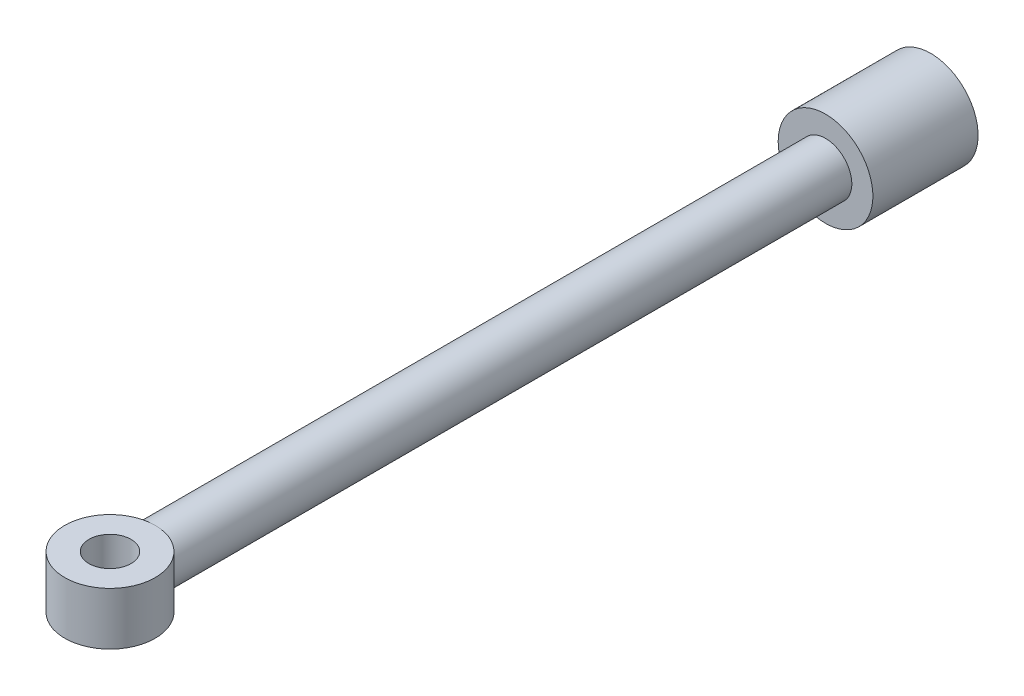
SolidWorks part; units mm, degrees
material "AISI 4340 Steel, normalized"
ref_plane "Front Plane" through (0, 0, 0) normal (0, 0, 1) x (1, 0, 0)
ref_plane "Top Plane" through (0, 0, 0) normal (0, 1, 0) x (1, 0, 0)
ref_plane "Right Plane" through (0, 0, 0) normal (1, 0, 0) x (0, 0, -1)
sketch "Sketch1" plane through (0, 0, 0) normal (0, 1, 0) x (1, 0, 0)
  line L0 (0, -75) -> (0, -855) construction
  line L1 (0, -75) -> (45, -75)
  line L4 (45, -75) -> (45, -175)
  line L5 (45, -175) -> (25, -175)
  line L6 (25, -175) -> (25, -820.0143)
  line L7 (25, -820.0143) -> (0, -820.0143)
  line L8 (0, -820.0143) -> (0, -75)
  circle A0 centre (0, -855) radius 20 construction
  circle A1 centre (0, -855) radius 43 construction
  circle A2 centre (0, 0) radius 20 construction
  dimension "D1" = 86
  dimension "D2" = 780
  dimension "D3" = 50
  dimension "D4" = 100
  dimension "D5" = 45
  dimension "D7" = 75
revolve "Revolve1" add sketch "Sketch1" angle 360 about L0
sketch "Sketch3" plane through (0, 0, 0) normal (0, 1, 0) x (1, 0, 0)
  circle A0 centre (0, -855) radius 20
  circle A1 centre (0, -855) radius 43
  circle A2 centre (0, -855) radius 43 construction
  circle A3 centre (0, -855) radius 20 construction
extrude "Boss-Extrude1" add sketch "Sketch3" along normal mid plane 50
